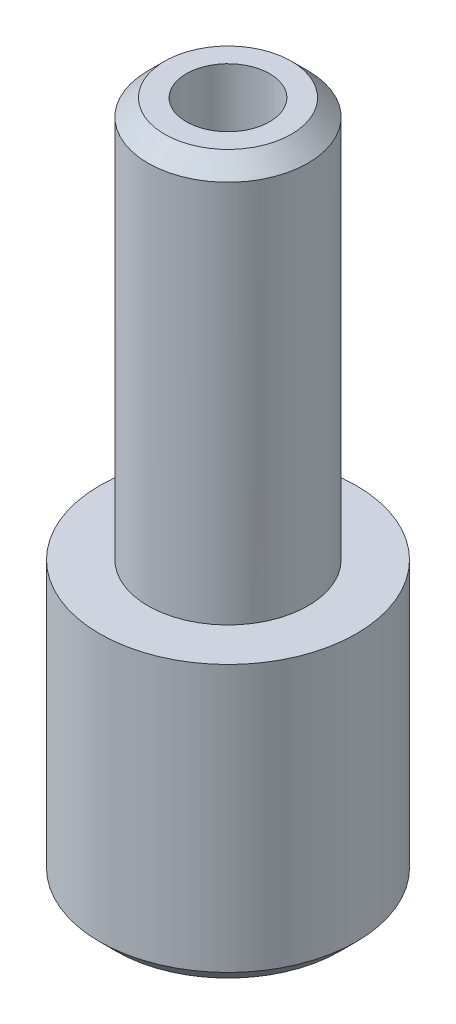
SolidWorks part; units mm, degrees
ref_plane "Front Plane" through (0, 0, 0) normal (0, 0, 1) x (1, 0, 0)
ref_plane "Top Plane" through (0, 0, 0) normal (0, 1, 0) x (1, 0, 0)
ref_plane "Right Plane" through (0, 0, 0) normal (1, 0, 0) x (0, 0, -1)
sketch "Sketch1" plane through (0, 0, 0) normal (0, 0, 1) x (1, 0, 0)
  line L0 (0, 9.7176) -> (0, -9.45) construction
  line L1 (1.25, 0) -> (1.25, 20.5)
  line L2 (1.25, 20.5) -> (2.4, 20.5)
  line L3 (2.4, 20.5) -> (2.4, 8.5)
  line L4 (2.4, 8.5) -> (3.85, 8.5)
  line L5 (3.85, 8.5) -> (3.85, 0)
  line L6 (3.85, 0) -> (1.25, 0)
  dimension "D1" = 7.7
  dimension "D2" = 4.8
  dimension "D3" = 2.5
  dimension "D4" = 8.5
  dimension "D5" = 12
revolve "Revolve1" add sketch "Sketch1" angle 360 about L0
chamfer "Chamfer1" distance 0.5 angle 45 2 edges at (-2.4, 20.5, 0) (-3.85, 0, 0)
